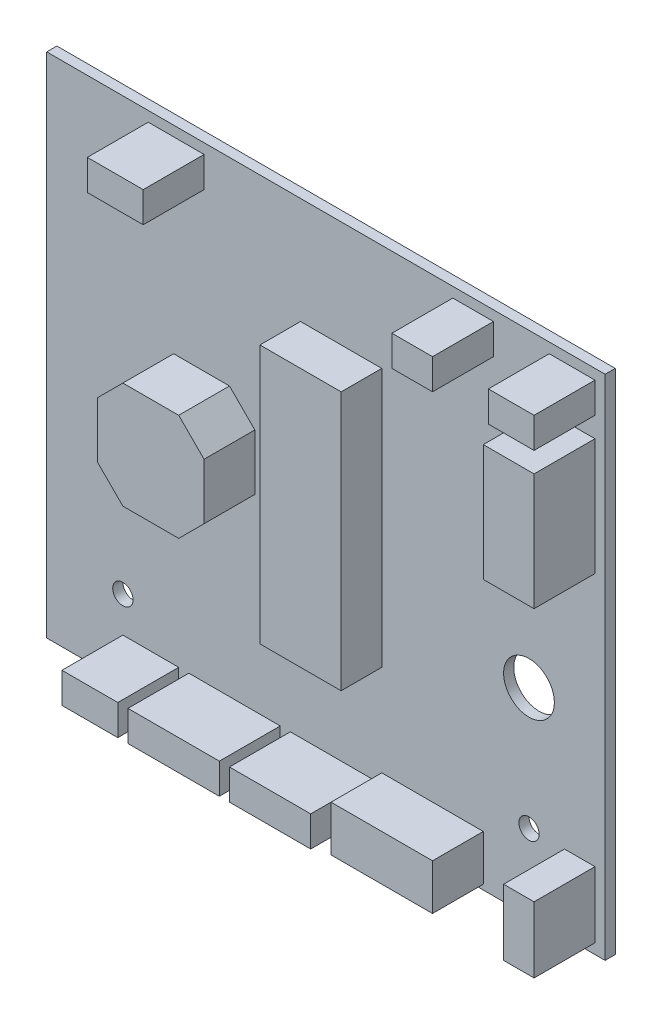
SolidWorks part; units mm, degrees
ref_plane "Plan de face" through (0, 0, 0) normal (0, 0, 1) x (1, 0, 0)
ref_plane "Plan de dessus" through (0, 0, 0) normal (0, 1, 0) x (1, 0, 0)
ref_plane "Plan de droite" through (0, 0, 0) normal (1, 0, 0) x (0, 0, -1)
sketch "Esquisse1" plane through (0, 0, 0) normal (0, 0, 1) x (1, 0, 0)
  line L1 (0, 0) -> (-110, 0)
  line L2 (0, 0) -> (0, 100)
  line L3 (0, 100) -> (-110, 100)
  line L4 (-110, 0) -> (-110, 100)
  dimension "D1" = 100
  dimension "D2" = 110
extrude "Extrusion1" add sketch "Esquisse1" along normal blind 2
sketch "Esquisse2" plane through (0, 0, 2) normal (0, 0, 1) x (1, 0, 0)
  line L0 (-55, 85) -> (-55, 100)
  line L1 (-95, 85) -> (-15, 85) construction
  line L2 (-95, 85) -> (-95, 15) construction
  line L3 (-95, 15) -> (-15, 15) construction
  line L4 (-15, 85) -> (-15, 15) construction
  line L5 (0, 100) -> (-110, 100) construction
  line L6 (-110, 50) -> (-95, 50)
  line L7 (-110, 100) -> (-110, 0) construction
  circle A0 centre (-95, 85) radius 2
  circle A1 centre (-15, 85) radius 2
  circle A2 centre (-15, 15) radius 2
  circle A3 centre (-95, 15) radius 2
  circle A4 centre (-15, 39) radius 5
  dimension "D3" = 4
  dimension "D4" = 10
  dimension "D5" = 24
  dimension "D1" = 80
  dimension "D2" = 70
extrude "Enlèv. mat.-Extru.1" cut sketch "Esquisse2" against normal blind 10 contours A4 | A2 | A1 | A3 | A0
sketch "Esquisse3" plane through (0, 0, 2) normal (0, 0, 1) x (1, 0, 0)
  line L1 (-95, 2) -> (-84, 2)
  line L2 (-95, 2) -> (-95, 8)
  line L3 (-95, 8) -> (-84, 8)
  line L4 (-84, 2) -> (-84, 8)
  line L5 (-82, 2) -> (-64, 2)
  line L6 (-82, 2) -> (-82, 8)
  line L7 (-82, 8) -> (-64, 8)
  line L8 (-64, 2) -> (-64, 8)
  line L9 (-62, 2) -> (-46, 2)
  line L10 (-62, 2) -> (-62, 8)
  line L11 (-62, 8) -> (-46, 8)
  line L12 (-46, 2) -> (-46, 8)
  line L13 (-8, 2) -> (-2, 2)
  line L14 (-8, 2) -> (-8, 15)
  line L15 (-8, 15) -> (-2, 15)
  line L16 (-2, 2) -> (-2, 15)
  line L17 (-2, 98) -> (-11, 98)
  line L18 (-2, 98) -> (-2, 92)
  line L19 (-2, 92) -> (-11, 92)
  line L20 (-11, 98) -> (-11, 92)
  line L21 (-2, 88) -> (-12, 88)
  line L22 (-2, 88) -> (-2, 65)
  line L23 (-2, 65) -> (-12, 65)
  line L24 (-12, 88) -> (-12, 65)
  line L25 (-22, 98) -> (-30, 98)
  line L26 (-22, 98) -> (-22, 92)
  line L27 (-22, 92) -> (-30, 92)
  line L28 (-30, 98) -> (-30, 92)
  line L29 (-79, 98) -> (-90, 98)
  line L30 (-79, 98) -> (-79, 92)
  line L31 (-79, 92) -> (-90, 92)
  line L32 (-90, 98) -> (-90, 92)
  line L33 (-60, 28) -> (-44, 28)
  line L34 (-60, 28) -> (-60, 79)
  line L35 (-60, 79) -> (-44, 79)
  line L36 (-44, 28) -> (-44, 79)
  line L37 (-90, 40) -> (-69, 40)
  line L38 (-90, 40) -> (-90, 61)
  line L39 (-90, 61) -> (-69, 61)
  line L40 (-69, 40) -> (-69, 61)
  line L41 (-110, 0) -> (0, 0) construction
  line L42 (0, 0) -> (0, 100) construction
  line L43 (0, 100) -> (-110, 100) construction
  line L44 (-44, 1) -> (-24, 1)
  line L45 (-44, 1) -> (-44, 10)
  line L46 (-44, 10) -> (-24, 10)
  line L47 (-24, 1) -> (-24, 10)
  line L48 (-110, 100) -> (-110, 0) construction
  dimension "D1" = 2
  dimension "D2" = 2
  dimension "D3" = 1
  dimension "D4" = 2
  dimension "D5" = 6
  dimension "D6" = 6
  dimension "D7" = 2
  dimension "D8" = 2
  dimension "D9" = 2
  dimension "D10" = 23
  dimension "D11" = 12
  dimension "D12" = 10
  dimension "D13" = 13
  dimension "D14" = 6
  dimension "D15" = 24
  dimension "D16" = 20
  dimension "D17" = 46
  dimension "D18" = 11
  dimension "D19" = 18
  dimension "D20" = 2
  dimension "D21" = 16
  dimension "D22" = 2
  dimension "D23" = 9
  dimension "D24" = 11
  dimension "D25" = 22
  dimension "D26" = 8
  dimension "D27" = 79
  dimension "D28" = 9
  dimension "D29" = 50
  dimension "D30" = 16
  dimension "D31" = 51
  dimension "D32" = 21
  dimension "D33" = 21
  dimension "D34" = 20
  dimension "D35" = 40
  dimension "D36" = 28
extrude "Extrusion2" add sketch "Esquisse3" along normal blind 12 contours L1 L4 L3 L2 | L5 L8 L7 L6 | L9 L12 L11 L10 | L13 L16 L15 L14 | L17 L20 L19 L18 | L25 L28 L27 L26 | L29 L32 L31 L30 | L44 L47 L46 L45 | L33 L36 L35 L34 | L37 L40 L39 L38 | L21 L24 L23 L22
sketch "Esquisse4" plane through (0, 0, 14) normal (0, 0, 1) x (1, 0, 0)
  line L1 (-90, 40) -> (-69, 40)
  line L2 (-90, 40) -> (-90, 61)
  line L3 (-90, 61) -> (-69, 61)
  line L4 (-69, 40) -> (-69, 61)
  line L5 (-44, 1) -> (-24, 1)
  line L6 (-44, 1) -> (-44, 10)
  line L7 (-44, 10) -> (-24, 10)
  line L8 (-24, 1) -> (-24, 10)
extrude "Enlèv. mat.-Extru.2" cut sketch "Esquisse4" against normal blind 2
sketch "Esquisse5" plane through (0, 0, 14) normal (0, 0, 1) x (1, 0, 0)
  line L1 (-60, 28) -> (-44, 28)
  line L2 (-60, 28) -> (-60, 79)
  line L3 (-60, 79) -> (-44, 79)
  line L4 (-44, 28) -> (-44, 79)
extrude "Enlèv. mat.-Extru.3" cut sketch "Esquisse5" against normal blind 4
chamfer "Chanfrein1" distance 5 angle 45 4 edges at (-90, 40, 7) (-90, 61, 7) (-69, 61, 7) (-69, 40, 7)
